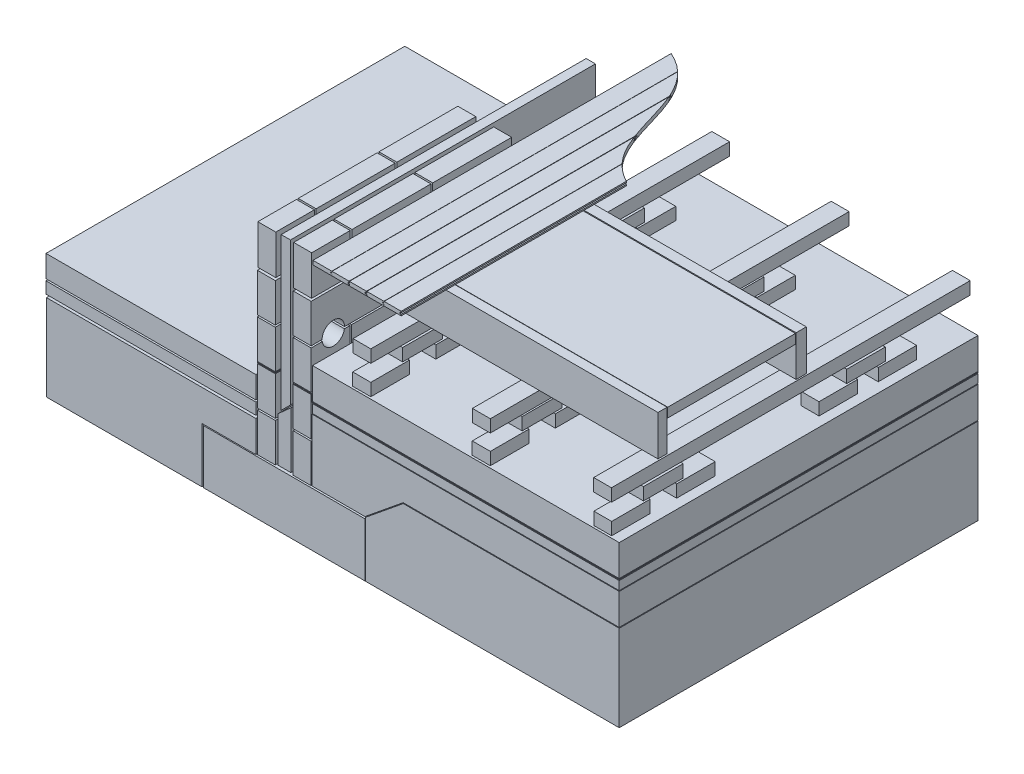
SolidWorks part; units mm, degrees
ref_plane "Front Plane" through (0, 0, 0) normal (0, 0, 1) x (1, 0, 0)
ref_plane "Top Plane" through (0, 0, 0) normal (0, 1, 0) x (1, 0, 0)
ref_plane "Right Plane" through (0, 0, 0) normal (1, 0, 0) x (0, 0, -1)
sketch "Sketch1" plane through (0, 0, 0) normal (0, 0, 1) x (1, 0, 0)
  line L0 (450, 300) -> (450, 963.876) construction
  line L1 (0, 0) -> (900, 0)
  line L2 (0, 0) -> (0, 300)
  line L3 (0, 300) -> (900, 300)
  line L4 (900, 0) -> (900, 300)
  dimension "D1" = 900
  dimension "D2" = 300
extrude "Extrude1" add sketch "Sketch1" against normal blind 2000
sketch "Sketch2" plane through (0, 0, 0) normal (0, 0, 1) x (1, 0, 0)
  line L0 (450, 300) -> (450, 793.4947) construction
  line L1 (900, 300) -> (0, 300) construction
  line L3 (400, 310) -> (300, 310)
  line L4 (400, 310) -> (400, 525)
  line L5 (400, 525) -> (300, 525)
  line L6 (300, 310) -> (300, 525)
  dimension "D1" = 100
  dimension "D2" = 215
  dimension "D3" = 10
  dimension "D4" = 50
extrude "Extrude2" add sketch "Sketch2" against normal blind 215 separate body
sketch "Sketch4" plane through (0, 0, 0) normal (0, 0, 1) x (1, 0, 0)
  line L0 (400, 525) -> (300, 525) construction
  line L1 (400, 535) -> (300, 535)
  line L2 (400, 535) -> (400, 750)
  line L3 (400, 750) -> (300, 750)
  line L4 (300, 535) -> (300, 750)
  dimension "D1" = 100
  dimension "D2" = 215
  dimension "D3" = 10
extrude "Extrude3" add sketch "Sketch4" against normal blind 440 separate body
sketch "Sketch5" plane through (400, 0, 0) normal (1, 0, 0) x (0, 0, -1)
  line L0 (2000, 300) -> (0, 300) construction
  line L1 (225, 525) -> (665, 525)
  line L2 (225, 525) -> (225, 310)
  line L3 (225, 310) -> (665, 310)
  line L4 (665, 525) -> (665, 310)
  line L5 (215, 310) -> (215, 525) construction
  line L6 (440, 535) -> (440, 750) construction
  line L7 (450, 535) -> (890, 535)
  line L8 (450, 535) -> (450, 750)
  line L9 (450, 750) -> (890, 750)
  line L10 (890, 535) -> (890, 750)
  line L12 (675, 525) -> (1115, 525)
  line L13 (675, 525) -> (675, 310)
  line L14 (675, 310) -> (1115, 310)
  line L15 (1115, 525) -> (1115, 310)
  line L16 (900, 750) -> (1340, 750)
  line L17 (900, 750) -> (900, 535)
  line L18 (900, 535) -> (1340, 535)
  line L19 (1340, 750) -> (1340, 535)
  line L20 (1125, 525) -> (1565, 525)
  line L21 (1125, 525) -> (1125, 310)
  line L22 (1125, 310) -> (1565, 310)
  line L23 (1565, 525) -> (1565, 310)
  line L24 (1350, 750) -> (1790, 750)
  line L25 (1350, 750) -> (1350, 535)
  line L26 (1350, 535) -> (1790, 535)
  line L27 (1790, 750) -> (1790, 535)
  line L28 (1575, 525) -> (2015, 525)
  line L29 (1575, 525) -> (1575, 310)
  line L30 (1575, 310) -> (2015, 310)
  line L31 (2015, 525) -> (2015, 310)
  dimension "D1" = 440
  dimension "D2" = 215
  dimension "D3" = 10
  dimension "D4" = 10
  dimension "D5" = 440
  dimension "D6" = 215
  dimension "D7" = 10
  dimension "D8" = 10
  dimension "D9" = 215
  dimension "D10" = 440
  dimension "D11" = 10
  dimension "D12" = 10
  dimension "D13" = 440
  dimension "D14" = 215
  dimension "D15" = 10
  dimension "D16" = 10
  dimension "D17" = 215
  dimension "D18" = 440
  dimension "D19" = 10
  dimension "D20" = 10
  dimension "D21" = 440
  dimension "D22" = 10
  dimension "D23" = 215
  dimension "D24" = 10
  dimension "D25" = 440
  dimension "D26" = 215
  dimension "D27" = 10
  dimension "D28" = 10
extrude "Extrude4" add sketch "Sketch5" against normal blind 100 separate body
sketch "Sketch8" plane through (0, 0, 0) normal (0, 0, 1) x (1, 0, 0)
  line L0 (400, 750) -> (300, 750) construction
  line L1 (300, 760) -> (400, 760)
  line L2 (300, 760) -> (300, 975)
  line L3 (300, 975) -> (400, 975)
  line L4 (400, 760) -> (400, 975)
  dimension "D1" = 215
  dimension "D2" = 100
  dimension "D3" = 10
extrude "Extrude5" add sketch "Sketch8" against normal blind 215 separate body
sketch "Sketch9" plane through (400, 0, 0) normal (1, 0, 0) x (0, 0, -1)
  line L0 (215, 760) -> (215, 975) construction
  line L1 (225, 975) -> (665, 975)
  line L2 (225, 975) -> (225, 760)
  line L3 (225, 760) -> (665, 760)
  line L4 (665, 975) -> (665, 760)
  line L5 (890, 750) -> (450, 750) construction
  line L6 (1340, 750) -> (900, 750) construction
  line L7 (675, 975) -> (1115, 975)
  line L8 (675, 975) -> (675, 760)
  line L9 (675, 760) -> (1115, 760)
  line L10 (1115, 975) -> (1115, 760)
  line L11 (215, 975) -> (0, 975) construction
  line L12 (0, 1200) -> (440, 1200)
  line L13 (0, 1200) -> (0, 985)
  line L14 (0, 985) -> (440, 985)
  line L15 (440, 1200) -> (440, 985)
  line L17 (450, 1200) -> (890, 1200)
  line L18 (450, 1200) -> (450, 985)
  line L19 (450, 985) -> (890, 985)
  line L20 (890, 1200) -> (890, 985)
  line L21 (1125, 975) -> (1565, 975)
  line L22 (1125, 975) -> (1125, 760)
  line L23 (1125, 760) -> (1565, 760)
  line L24 (1565, 975) -> (1565, 760)
  line L25 (900, 1200) -> (1340, 1200)
  line L26 (900, 1200) -> (900, 985)
  line L27 (900, 985) -> (1340, 985)
  line L28 (1340, 1200) -> (1340, 985)
  dimension "D1" = 440
  dimension "D2" = 215
  dimension "D3" = 10
  dimension "D4" = 10
  dimension "D5" = 215
  dimension "D6" = 10
  dimension "D7" = 10
  dimension "D8" = 440
  dimension "D9" = 215
  dimension "D10" = 10
  dimension "D11" = 440
  dimension "D12" = 10
  dimension "D13" = 215
  dimension "D14" = 10
  dimension "D15" = 440
  dimension "D16" = 440
  dimension "D17" = 10
  dimension "D18" = 440
  dimension "D19" = 10
extrude "Extrude6" add sketch "Sketch9" against normal blind 100 separate body
sketch "Sketch10" plane through (0, 0, 0) normal (0, 0, 1) x (1, 0, 0)
  line L0 (900, 300) -> (0, 300) construction
  line L1 (500, 525) -> (600, 525)
  line L2 (500, 525) -> (500, 310)
  line L3 (500, 310) -> (600, 310)
  line L4 (600, 525) -> (600, 310)
  line L5 (400, 310) -> (400, 525) construction
  dimension "D1" = 100
  dimension "D2" = 215
  dimension "D3" = 10
  dimension "D4" = 100
extrude "Extrude7" add sketch "Sketch10" against normal blind 215 separate body
sketch "Sketch12" plane through (600, 0, 0) normal (1, 0, 0) x (0, 0, -1)
  line L1 (225, 525) -> (665, 525)
  line L2 (225, 525) -> (225, 310)
  line L3 (225, 310) -> (665, 310)
  line L4 (665, 525) -> (665, 310)
extrude "Extrude9" add sketch "Sketch12" against normal blind 100 separate body
sketch "Sketch13" plane through (600, 0, 0) normal (1, 0, 0) x (0, 0, -1)
  line L0 (1575, 310) -> (2015, 310) construction
  line L1 (675, 525) -> (1115, 525)
  line L2 (675, 525) -> (675, 310)
  line L3 (675, 310) -> (1115, 310)
  line L4 (1115, 525) -> (1115, 310)
  line L5 (1565, 525) -> (1125, 525)
  line L6 (1565, 525) -> (1565, 310)
  line L7 (1565, 310) -> (1125, 310)
  line L8 (1125, 525) -> (1125, 310)
  line L9 (2015, 525) -> (1575, 525)
  line L10 (2015, 525) -> (2015, 310)
  line L11 (2015, 310) -> (1575, 310)
  line L12 (1575, 525) -> (1575, 310)
  line L13 (890, 535) -> (890, 750) construction
  line L14 (1790, 750) -> (1350, 750)
  line L15 (1790, 750) -> (1790, 535)
  line L16 (1790, 535) -> (1350, 535)
  line L17 (1350, 750) -> (1350, 535)
  line L18 (1340, 750) -> (900, 750)
  line L19 (1340, 750) -> (1340, 535)
  line L20 (1340, 535) -> (900, 535)
  line L21 (900, 750) -> (900, 535)
  line L22 (450, 750) -> (890, 750)
  line L23 (450, 750) -> (450, 535)
  line L24 (450, 535) -> (890, 535)
  line L25 (890, 750) -> (890, 535)
  line L26 (450, 535) -> (890, 535) construction
  line L27 (440, 535) -> (0, 535) construction
  line L28 (0, 750) -> (440, 750)
  line L29 (0, 750) -> (0, 535)
  line L30 (0, 535) -> (440, 535)
  line L31 (440, 750) -> (440, 535)
  line L32 (440, 535) -> (440, 750) construction
extrude "Extrude10" add sketch "Sketch13" against normal blind 100 separate body
sketch "Sketch14" plane through (600, 0, 0) normal (1, 0, 0) x (0, 0, -1)
  line L0 (215, 760) -> (215, 975) construction
  line L1 (0, 975) -> (215, 975)
  line L2 (0, 975) -> (0, 760)
  line L3 (0, 760) -> (215, 760)
  line L4 (215, 975) -> (215, 760)
  line L5 (225, 760) -> (665, 760) construction
  line L6 (665, 975) -> (225, 975)
  line L7 (665, 975) -> (665, 760)
  line L8 (665, 760) -> (225, 760)
  line L9 (225, 975) -> (225, 760)
  line L10 (1125, 975) -> (1125, 760) construction
  line L11 (1115, 975) -> (675, 975)
  line L12 (1115, 975) -> (1115, 760)
  line L13 (1115, 760) -> (675, 760)
  line L14 (675, 975) -> (675, 760)
  line L15 (1565, 975) -> (1125, 975)
  line L16 (1565, 975) -> (1565, 760)
  line L17 (1565, 760) -> (1125, 760)
  line L18 (1125, 975) -> (1125, 760)
  line L19 (1125, 760) -> (1565, 760) construction
  line L21 (1340, 1200) -> (900, 1200)
  line L22 (1340, 1200) -> (1340, 985)
  line L23 (1340, 985) -> (900, 985)
  line L24 (900, 1200) -> (900, 985)
  line L25 (450, 1200) -> (890, 1200)
  line L26 (450, 1200) -> (450, 985)
  line L27 (450, 985) -> (890, 985)
  line L28 (890, 1200) -> (890, 985)
  line L29 (0, 1200) -> (440, 1200)
  line L30 (0, 1200) -> (0, 985)
  line L31 (0, 985) -> (440, 985)
  line L32 (440, 1200) -> (440, 985)
extrude "Extrude11" add sketch "Sketch14" against normal blind 100 separate body
sketch "Sketch15" plane through (0, 0, 0) normal (0, 0, 1) x (1, 0, 0)
  line L0 (484.509, 1198.9771) -> (484.509, 641.9037)
  line L1 (484.509, 641.9037) -> (432.7455, 590.1403)
  line L2 (432.7455, 590.1403) -> (432.7455, 1208.6688)
  line L3 (484.509, 1198.9771) -> (484.509, 1438.6688)
  line L4 (484.509, 1438.6688) -> (432.7455, 1438.6688)
  line L5 (432.7455, 1438.6688) -> (432.7455, 1208.6688)
  dimension "D1" = 230
extrude "Extrude12" add sketch "Sketch15" against normal blind 1700
sketch "Sketch16" plane through (0, 0, 0) normal (0, 0, 1) x (1, 0, 0)
  line L0 (486.9739, 629.5791) -> (486.9739, 316.5335)
  line L1 (486.9739, 316.5335) -> (415.491, 316.5335)
  line L2 (415.491, 316.5335) -> (415.491, 565.491)
  line L3 (415.491, 565.491) -> (486.9739, 629.5791)
extrude "Extrude13" add sketch "Sketch16" against normal blind 1904 separate body
sketch "Sketch17" plane through (0, 0, 0) normal (0, 0, 1) x (1, 0, 0)
  line L3 (903.1057, 300) -> (2317.0911, 300)
  line L4 (903.1057, 300) -> (903.1057, 0)
  line L5 (903.1057, 0) -> (2317.0911, 0)
  line L6 (2317.0911, 300) -> (2317.0911, 0)
extrude "Extrude14" add sketch "Sketch17" against normal blind 2000 separate body
sketch "Sketch18" plane through (0, 0, 0) normal (0, 0, 1) x (1, 0, 0)
  line L0 (603.8197, 310.918) -> (603.8197, 658.0545)
  line L1 (603.8197, 658.0545) -> (2317.0911, 658.0545)
  line L2 (2317.0911, 658.0545) -> (2317.0911, 484.4863)
  line L3 (2317.0911, 484.4863) -> (1112.869, 484.4863)
  line L4 (1112.869, 484.4863) -> (899.8103, 310.918)
  line L5 (899.8103, 310.918) -> (603.8197, 310.918)
extrude "Extrude15" add sketch "Sketch18" against normal blind 2000 separate body
sketch "Sketch19" plane through (0, 0, 0) normal (0, 0, 1) x (1, 0, 0)
  line L0 (2317.0911, 300) -> (2317.0911, 480.3446)
  line L1 (2317.0911, 480.3446) -> (1113.2002, 480.3446)
  line L2 (1113.2002, 480.3446) -> (903.1057, 308.9106)
  line L3 (903.1057, 308.9106) -> (903.1057, 300)
  line L4 (903.1057, 300) -> (2317.0911, 300)
extrude "Extrude16" add sketch "Sketch19" against normal blind 2000
sketch "Sketch20" plane through (0, 0, 0) normal (0, 0, 1) x (1, 0, 0)
  line L0 (2317.0911, 484.4863) -> (2317.0911, 658.0545) construction
  line L1 (607.0688, 661.8486) -> (2317.0911, 661.8486)
  line L2 (607.0688, 661.8486) -> (607.0688, 710.335)
  line L3 (607.0688, 710.335) -> (2317.0911, 710.335)
  line L4 (2317.0911, 661.8486) -> (2317.0911, 710.335)
extrude "Extrude17" add sketch "Sketch20" against normal blind 2000 separate body
sketch "Sketch24" plane through (0, 0, 0) normal (0, 0, 1) x (1, 0, 0)
  line L0 (499.4544, 757.3771) -> (605.5978, 757.3771)
  line L1 (605.5978, 757.3771) -> (605.5978, 718.0647)
  line L2 (605.5978, 718.0647) -> (2317.0911, 718.0647)
  line L3 (2317.0911, 718.0647) -> (2317.0911, 714.4218)
  line L4 (2317.0911, 714.4218) -> (601.8753, 714.4218)
  line L5 (601.8753, 714.4218) -> (601.8753, 752.4529)
  line L6 (601.8753, 752.4529) -> (499.4544, 752.4529)
  line L7 (499.4544, 752.4529) -> (499.4544, 757.3771)
extrude "Extrude20" add sketch "Sketch24" against normal blind 2000 separate body
sketch "Sketch25" plane through (0, 0, 0) normal (0, 0, 1) x (1, 0, 0)
  line L1 (607.4398, 720.2347) -> (2317.0911, 720.2347)
  line L2 (607.4398, 720.2347) -> (607.4398, 893.8313)
  line L3 (607.4398, 893.8313) -> (2317.0911, 893.8313)
  line L4 (2317.0911, 720.2347) -> (2317.0911, 893.8313)
extrude "Extrude21" add sketch "Sketch25" against normal blind 2000 separate body
sketch "Sketch28" plane through (0, 0, 0) normal (0, 0, 1) x (1, 0, 0)
  line L1 (831.5046, 905.5968) -> (932.3555, 905.5968)
  line L2 (831.5046, 905.5968) -> (831.5046, 975.0351)
  line L3 (831.5046, 975.0351) -> (932.3555, 975.0351)
  line L4 (932.3555, 905.5968) -> (932.3555, 975.0351)
  line L5 (1497.7817, 975.0351) -> (1598.6326, 975.0351)
  line L6 (1497.7817, 975.0351) -> (1497.7817, 905.5968)
  line L7 (1497.7817, 905.5968) -> (1598.6326, 905.5968)
  line L8 (1598.6326, 975.0351) -> (1598.6326, 905.5968)
  line L9 (2175.8669, 975.0351) -> (2274.889, 975.0351)
  line L10 (2175.8669, 975.0351) -> (2175.8669, 905.5968)
  line L11 (2175.8669, 905.5968) -> (2274.889, 905.5968)
  line L12 (2274.889, 975.0351) -> (2274.889, 905.5968)
extrude "Extrude23" add sketch "Sketch28" against normal blind 215 separate body
sketch "Sketch29" plane through (2274.889, 0, 0) normal (1, 0, 0) x (0, 0, -1)
  line L0 (665, 975) -> (225, 975) construction
  line L1 (362.2188, 975) -> (577.3125, 975)
  line L2 (362.2188, 975) -> (362.2188, 905.9784)
  line L3 (362.2188, 905.9784) -> (577.3125, 905.9784)
  line L4 (577.3125, 975) -> (577.3125, 905.9784)
  line L5 (1565, 975) -> (1125, 975) construction
  line L6 (1155.945, 975) -> (1371.0387, 975)
  line L7 (1155.945, 975) -> (1155.945, 905.9784)
  line L8 (1155.945, 905.9784) -> (1371.0387, 905.9784)
  line L9 (1371.0387, 975) -> (1371.0387, 905.9784)
  line L10 (1486.1593, 975) -> (1700, 975)
  line L11 (1486.1593, 975) -> (1486.1593, 905.9784)
  line L12 (1486.1593, 905.9784) -> (1700, 905.9784)
  line L13 (1700, 975) -> (1700, 905.9784)
  line L14 (1700, 641.9037) -> (1700, 1438.6688) construction
extrude "Extrude24" add sketch "Sketch29" against normal blind 100 separate body
sketch "Sketch30" plane through (1598.6326, 0, 0) normal (1, 0, 0) x (0, 0, -1)
  line L1 (362.2188, 975) -> (577.3125, 975)
  line L2 (362.2188, 975) -> (362.2188, 905.9784)
  line L3 (362.2188, 905.9784) -> (577.3125, 905.9784)
  line L4 (577.3125, 975) -> (577.3125, 905.9784)
  line L5 (1155.945, 975) -> (1371.0387, 975)
  line L6 (1155.945, 975) -> (1155.945, 905.9784)
  line L7 (1155.945, 905.9784) -> (1371.0387, 905.9784)
  line L8 (1371.0387, 975) -> (1371.0387, 905.9784)
  line L9 (1486.1593, 975) -> (1700, 975)
  line L10 (1486.1593, 975) -> (1486.1593, 905.9784)
  line L11 (1486.1593, 905.9784) -> (1700, 905.9784)
  line L12 (1700, 975) -> (1700, 905.9784)
extrude "Extrude25" add sketch "Sketch30" against normal blind 100 separate body
sketch "Sketch31" plane through (932.3555, 0, 0) normal (1, 0, 0) x (0, 0, -1)
  line L0 (362.2188, 905.9784) -> (577.3125, 905.9784) construction
  line L1 (577.3125, 975) -> (362.2188, 975)
  line L2 (577.3125, 975) -> (577.3125, 905.9784)
  line L3 (577.3125, 905.9784) -> (362.2188, 905.9784)
  line L4 (362.2188, 975) -> (362.2188, 905.9784)
  line L5 (362.2188, 975) -> (362.2188, 905.9784) construction
  line L6 (1486.1593, 975) -> (1486.1593, 905.9784) construction
  line L7 (1371.0387, 975) -> (1155.945, 975)
  line L8 (1371.0387, 975) -> (1371.0387, 905.9784)
  line L9 (1371.0387, 905.9784) -> (1155.945, 905.9784)
  line L10 (1155.945, 975) -> (1155.945, 905.9784)
  line L11 (1700, 975) -> (1486.1593, 975)
  line L12 (1700, 975) -> (1700, 905.9784)
  line L13 (1700, 905.9784) -> (1486.1593, 905.9784)
  line L14 (1486.1593, 975) -> (1486.1593, 905.9784)
extrude "Extrude26" add sketch "Sketch31" against normal blind 100 separate body
sketch "Sketch32" plane through (2274.889, 0, 0) normal (1, 0, 0) x (0, 0, -1)
  line L0 (0, 985) -> (440, 985) construction
  line L1 (177.42, 1054.4234) -> (398.5727, 1054.4234)
  line L2 (177.42, 1054.4234) -> (177.42, 985)
  line L3 (177.42, 985) -> (398.5727, 985)
  line L4 (398.5727, 1054.4234) -> (398.5727, 985)
  line L6 (1310.4489, 1054.4234) -> (1525.5427, 1054.4234)
  line L7 (1310.4489, 1054.4234) -> (1310.4489, 985)
  line L8 (1310.4489, 985) -> (1525.5427, 985)
  line L9 (1525.5427, 1054.4234) -> (1525.5427, 985)
extrude "Extrude27" add sketch "Sketch32" against normal blind 100 separate body
sketch "Sketch33" plane through (1598.6326, 0, 0) normal (1, 0, 0) x (0, 0, -1)
  line L1 (398.5727, 1054.4234) -> (177.42, 1054.4234)
  line L2 (398.5727, 1054.4234) -> (398.5727, 985)
  line L3 (398.5727, 985) -> (177.42, 985)
  line L4 (177.42, 1054.4234) -> (177.42, 985)
  line L5 (1525.5427, 1054.4234) -> (1310.4489, 1054.4234)
  line L6 (1525.5427, 1054.4234) -> (1525.5427, 985)
  line L7 (1525.5427, 985) -> (1310.4489, 985)
  line L8 (1310.4489, 1054.4234) -> (1310.4489, 985)
extrude "Extrude28" add sketch "Sketch33" against normal blind 100 separate body
sketch "Sketch34" plane through (932.3555, 0, 0) normal (1, 0, 0) x (0, 0, -1)
  line L1 (398.5727, 1054.4234) -> (177.42, 1054.4234)
  line L2 (398.5727, 1054.4234) -> (398.5727, 985)
  line L3 (398.5727, 985) -> (177.42, 985)
  line L4 (177.42, 1054.4234) -> (177.42, 985)
  line L5 (1525.5427, 1054.4234) -> (1310.4489, 1054.4234)
  line L6 (1525.5427, 1054.4234) -> (1525.5427, 985)
  line L7 (1525.5427, 985) -> (1310.4489, 985)
  line L8 (1310.4489, 1054.4234) -> (1310.4489, 985)
extrude "Extrude29" add sketch "Sketch34" against normal blind 100 separate body
sketch "Sketch35" plane through (0, 0, 0) normal (0, 0, 1) x (1, 0, 0)
  line L1 (2174.889, 1066.7649) -> (2273.7044, 1066.7649)
  line L2 (2174.889, 1066.7649) -> (2174.889, 1136.9347)
  line L3 (2174.889, 1136.9347) -> (2273.7044, 1136.9347)
  line L4 (2273.7044, 1066.7649) -> (2273.7044, 1136.9347)
extrude "Extrude30" add sketch "Sketch35" against normal up to vertex (2000 mm away) separate body
sketch "Sketch36" plane through (0, 0, 0) normal (0, 0, 1) x (1, 0, 0)
  line L1 (1598.6326, 1063.4688) -> (1498.6326, 1063.4688)
  line L2 (1598.6326, 1063.4688) -> (1598.6326, 1132.5872)
  line L3 (1598.6326, 1132.5872) -> (1498.6326, 1132.5872)
  line L4 (1498.6326, 1063.4688) -> (1498.6326, 1132.5872)
extrude "Extrude31" add sketch "Sketch36" against normal up to vertex (2000 mm away) separate body
sketch "Sketch37" plane through (0, 0, 0) normal (0, 0, 1) x (1, 0, 0)
  line L1 (932.3555, 1066.7692) -> (833.3521, 1066.7692)
  line L2 (932.3555, 1066.7692) -> (932.3555, 1136.7531)
  line L3 (932.3555, 1136.7531) -> (833.3521, 1136.7531)
  line L4 (833.3521, 1066.7692) -> (833.3521, 1136.7531)
extrude "Extrude32" add sketch "Sketch37" against normal up to vertex (2000 mm away) separate body
sketch "Sketch39" plane through (300, 0, 0) normal (-1, 0, 0) x (0, 0, 1)
  line L1 (-2.5876, 1213.1316) -> (-217.5876, 1213.1316)
  line L2 (-2.5876, 1213.1316) -> (-2.5876, 1433.1316)
  line L3 (-2.5876, 1433.1316) -> (-217.5876, 1433.1316)
  line L4 (-217.5876, 1213.1316) -> (-217.5876, 1433.1316)
  line L5 (-227.5876, 1213.1316) -> (-667.5876, 1213.1316)
  line L6 (-227.5876, 1213.1316) -> (-227.5876, 1433.1316)
  line L7 (-227.5876, 1433.1316) -> (-667.5876, 1433.1316)
  line L8 (-667.5876, 1213.1316) -> (-667.5876, 1433.1316)
  line L9 (-677.5876, 1213.1316) -> (-1117.5876, 1213.1316)
  line L10 (-677.5876, 1213.1316) -> (-677.5876, 1433.1316)
  line L11 (-677.5876, 1433.1316) -> (-1117.5876, 1433.1316)
  line L12 (-1117.5876, 1213.1316) -> (-1117.5876, 1433.1316)
  dimension "D1" = 220
  dimension "D2" = 440
  dimension "D3" = 440
  dimension "D4" = 10
  dimension "D5" = 10
extrude "Extrude33" add sketch "Sketch39" against normal blind 100 separate body
sketch "Sketch40" plane through (600, 0, 0) normal (1, 0, 0) x (0, 0, -1)
  line L0 (1117.5876, 1433.1316) -> (1117.5876, 1213.1316) construction
  line L1 (2.5876, 1433.1316) -> (217.5876, 1433.1316)
  line L2 (2.5876, 1433.1316) -> (2.5876, 1213.1316)
  line L3 (2.5876, 1213.1316) -> (217.5876, 1213.1316)
  line L4 (217.5876, 1433.1316) -> (217.5876, 1213.1316)
  line L5 (667.5876, 1213.1316) -> (227.5876, 1213.1316)
  line L6 (667.5876, 1213.1316) -> (667.5876, 1433.1316)
  line L7 (667.5876, 1433.1316) -> (227.5876, 1433.1316)
  line L8 (227.5876, 1213.1316) -> (227.5876, 1433.1316)
  line L9 (677.5876, 1433.1316) -> (1117.5876, 1433.1316)
  line L10 (677.5876, 1433.1316) -> (677.5876, 1213.1316)
  line L11 (677.5876, 1213.1316) -> (1117.5876, 1213.1316)
  line L12 (1117.5876, 1433.1316) -> (1117.5876, 1213.1316)
extrude "Extrude34" add sketch "Sketch40" against normal blind 100 separate body
sketch "Sketch41" plane through (0, 0, 0) normal (0, 0, 1) x (1, 0, 0)
  line L0 (291.4636, 480.3446) -> (-875.8625, 480.3446)
  line L1 (-875.8625, 480.3446) -> (-875.8625, 0)
  line L2 (-875.8625, 0) -> (-8.8472, 0)
  line L3 (-8.8472, 0) -> (-8.8472, 305.9207)
  line L4 (-8.8472, 305.9207) -> (291.4636, 305.9207)
  line L5 (291.4636, 305.9207) -> (291.4636, 480.3446)
extrude "Extrude35" add sketch "Sketch41" against normal up to vertex (2000 mm away) separate body
sketch "Sketch42" plane through (0, 0, 0) normal (0, 0, 1) x (1, 0, 0)
  line L0 (-878.2333, 495.6626) -> (-878.2333, 559.7833)
  line L1 (291.4636, 495.6626) -> (-878.2333, 495.6626)
  line L2 (-878.2333, 559.7833) -> (291.4636, 559.7833)
  line L3 (291.4636, 559.7833) -> (291.4636, 495.6626)
extrude "Extrude36" add sketch "Sketch42" against normal up to vertex (2000 mm away) separate body
sketch "Sketch43" plane through (0, 0, 0) normal (0, 0, 1) x (1, 0, 0)
  line L1 (-878.2333, 569.9251) -> (291.4636, 569.9251)
  line L2 (-878.2333, 569.9251) -> (-878.2333, 692.3537)
  line L3 (-878.2333, 692.3537) -> (291.4636, 692.3537)
  line L4 (291.4636, 569.9251) -> (291.4636, 692.3537)
extrude "Extrude37" add sketch "Sketch43" against normal up to vertex (2000 mm away) separate body
sketch "Sketch44" plane through (0, 0, 0) normal (0, 0, 1) x (1, 0, 0)
  line L1 (399.6407, 757.6392) -> (300.1046, 757.6392)
  line L2 (399.6407, 757.6392) -> (399.6407, 753.2349)
  line L3 (399.6407, 753.2349) -> (300.1046, 753.2349)
  line L4 (300.1046, 757.6392) -> (300.1046, 753.2349)
extrude "Extrude38" add sketch "Sketch44" against normal up to vertex (1790 mm away) separate body
sketch "Sketch45" plane through (2273.7044, 0, 0) normal (1, 0, 0) x (0, 0, -1)
  line L1 (259.5638, 1146.1094) -> (310.704, 1146.1094)
  line L2 (259.5638, 1146.1094) -> (259.5638, 1370.558)
  line L3 (259.5638, 1370.558) -> (310.704, 1370.558)
  line L4 (310.704, 1146.1094) -> (310.704, 1370.558)
extrude "Extrude39" add sketch "Sketch45" against normal blind 1665 separate body
sketch "Sketch46" plane through (2273.7044, 0, 0) normal (1, 0, 0) x (0, 0, -1)
  line L1 (1029.5574, 1370.558) -> (1086.2763, 1370.558)
  line L2 (1029.5574, 1370.558) -> (1029.5574, 1144.7265)
  line L3 (1029.5574, 1144.7265) -> (1086.2763, 1144.7265)
  line L4 (1086.2763, 1370.558) -> (1086.2763, 1144.7265)
extrude "Extrude40" add sketch "Sketch46" against normal blind 1665 separate body
sketch "Sketch47" plane through (0, 0, -2.5876) normal (0, 0, 1) x (1, 0, 0)
  line L0 (607.5373, 1378.052) -> (712.1577, 1378.052)
  line L1 (712.1577, 1378.052) -> (712.1577, 1385.5249)
  line L2 (712.1577, 1385.5249) -> (704.6848, 1385.5249)
  line L3 (704.6848, 1385.5249) -> (704.6848, 1392.9978)
  line L4 (704.6848, 1392.9978) -> (712.1577, 1392.9978)
  line L5 (712.1577, 1392.9978) -> (712.1577, 1400.4707)
  line L6 (712.1577, 1400.4707) -> (607.5373, 1400.4707)
  line L7 (607.5373, 1400.4707) -> (607.5373, 1378.052)
  line L8 (713.483, 1400.4707) -> (713.483, 1391.5015)
  line L9 (713.483, 1391.5015) -> (705.1984, 1391.5015)
  line L10 (705.1984, 1391.5015) -> (705.1984, 1386.1891)
  line L11 (705.1984, 1386.1891) -> (713.483, 1386.1891)
  line L12 (713.483, 1386.1891) -> (713.483, 1378.052)
  line L13 (713.483, 1378.052) -> (808.4949, 1378.052)
  line L14 (808.4949, 1378.052) -> (808.4949, 1385.5249)
  line L15 (808.4949, 1385.5249) -> (801.3597, 1385.5249)
  line L16 (801.3597, 1385.5249) -> (801.3597, 1392.9978)
  line L17 (801.3597, 1392.9978) -> (808.4949, 1392.9978)
  line L18 (808.4949, 1392.9978) -> (808.4949, 1400.4707)
  line L19 (808.4949, 1400.4707) -> (713.483, 1400.4707)
  line L20 (898.3168, 1392.9978) -> (905.4521, 1392.9978)
  line L21 (802.1555, 1391.5015) -> (802.1555, 1386.1891)
  line L22 (905.4521, 1385.5249) -> (898.3168, 1385.5249)
  line L23 (810.4401, 1391.5015) -> (802.1555, 1391.5015)
  line L24 (810.4401, 1400.4707) -> (810.4401, 1391.5015)
  line L25 (802.1555, 1386.1891) -> (810.4401, 1386.1891)
  line L26 (905.4521, 1378.052) -> (905.4521, 1385.5249)
  line L27 (810.4401, 1378.052) -> (905.4521, 1378.052)
  line L28 (898.3168, 1385.5249) -> (898.3168, 1392.9978)
  line L29 (905.4521, 1400.4707) -> (810.4401, 1400.4707)
  line L30 (810.4401, 1386.1891) -> (810.4401, 1378.052)
  line L31 (905.4521, 1392.9978) -> (905.4521, 1400.4707)
  line L32 (1002.6131, 1392.9978) -> (1002.6131, 1400.4707)
  line L33 (907.6011, 1391.5015) -> (899.3165, 1391.5015)
  line L34 (899.3165, 1391.5015) -> (899.3165, 1386.1891)
  line L35 (1002.6131, 1378.052) -> (1002.6131, 1385.5249)
  line L36 (1002.6131, 1400.4707) -> (907.6011, 1400.4707)
  line L37 (995.4778, 1392.9978) -> (1002.6131, 1392.9978)
  line L38 (907.6011, 1400.4707) -> (907.6011, 1391.5015)
  line L39 (907.6011, 1386.1891) -> (907.6011, 1378.052)
  line L40 (899.3165, 1386.1891) -> (907.6011, 1386.1891)
  line L41 (907.6011, 1378.052) -> (1002.6131, 1378.052)
  line L42 (1002.6131, 1385.5249) -> (995.4778, 1385.5249)
  line L43 (995.4778, 1385.5249) -> (995.4778, 1392.9978)
  line L44 (1091.9929, 1392.9978) -> (1099.1281, 1392.9978)
  line L45 (995.8316, 1391.5015) -> (995.8316, 1386.1891)
  line L46 (1099.1281, 1378.052) -> (1099.1281, 1385.5249)
  line L47 (1099.1281, 1385.5249) -> (1091.9929, 1385.5249)
  line L48 (1099.1281, 1400.4707) -> (1004.1162, 1400.4707)
  line L49 (1004.1162, 1400.4707) -> (1004.1162, 1391.5015)
  line L50 (1099.1281, 1392.9978) -> (1099.1281, 1400.4707)
  line L51 (1004.1162, 1391.5015) -> (995.8316, 1391.5015)
  line L52 (995.8316, 1386.1891) -> (1004.1162, 1386.1891)
  line L53 (1004.1162, 1386.1891) -> (1004.1162, 1378.052)
  line L54 (1004.1162, 1378.052) -> (1099.1281, 1378.052)
  line L55 (1091.9929, 1385.5249) -> (1091.9929, 1392.9978)
extrude "Extrude42" add sketch "Sketch47" against normal up to vertex (1997.4124 mm away) separate body
sketch "Sketch48" plane through (0, 1400.4707, 0) normal (0, 1, 0) x (1, 0, 0)
  line L0 (802.1555, 2000) -> (802.1555, 2.5876) construction
  line L1 (1099.1281, 2000) -> (1099.1281, 2.5876) construction
  line L2 (605.5978, 2000) -> (1099.1281, 2000)
  line L3 (1099.1281, 2000) -> (1099.1281, 1257.3421)
  spline S0 degree 3 poles (605.5978, 2000) (935.0084, 1857.1736) (794.9526, 1415.8535) (1099.1281, 1257.3421) knots 0 0 0 0 1 1 1 1
extrude "Extrude43" cut sketch "Sketch48" against normal blind 23
sketch "Sketch49" plane through (2273.7044, 0, 0) normal (1, 0, 0) x (0, 0, -1)
  line L1 (313.8498, 1369.0648) -> (1025.6776, 1369.0648)
  line L2 (313.8498, 1369.0648) -> (313.8498, 1316.7245)
  line L3 (313.8498, 1316.7245) -> (1025.6776, 1316.7245)
  line L4 (1025.6776, 1369.0648) -> (1025.6776, 1316.7245)
extrude "Extrude44" add sketch "Sketch49" against normal up to vertex (1665 mm away) separate body
sketch "Sketch50" plane through (300, 0, 0) normal (-1, 0, 0) x (0, 0, 1)
  line L0 (0, 985) -> (-440, 985) construction
  circle A0 centre (-123.482, 985) radius 62.5984
extrude "Extrude46" cut sketch "Sketch50" against normal blind 300
sketch "Sketch51" plane through (0, 0, -259.5638) normal (0, 0, 1) x (1, 0, 0)
  line L0 (608.7044, 1370.558) -> (649.276, 1146.1094)
  line L1 (608.7044, 1146.1094) -> (2273.7044, 1146.1094) construction
  line L2 (649.276, 1146.1094) -> (608.7044, 1146.1094)
  line L3 (608.7044, 1146.1094) -> (608.7044, 1370.558)
extrude "Extrude47" cut sketch "Sketch51" against normal up to vertex
